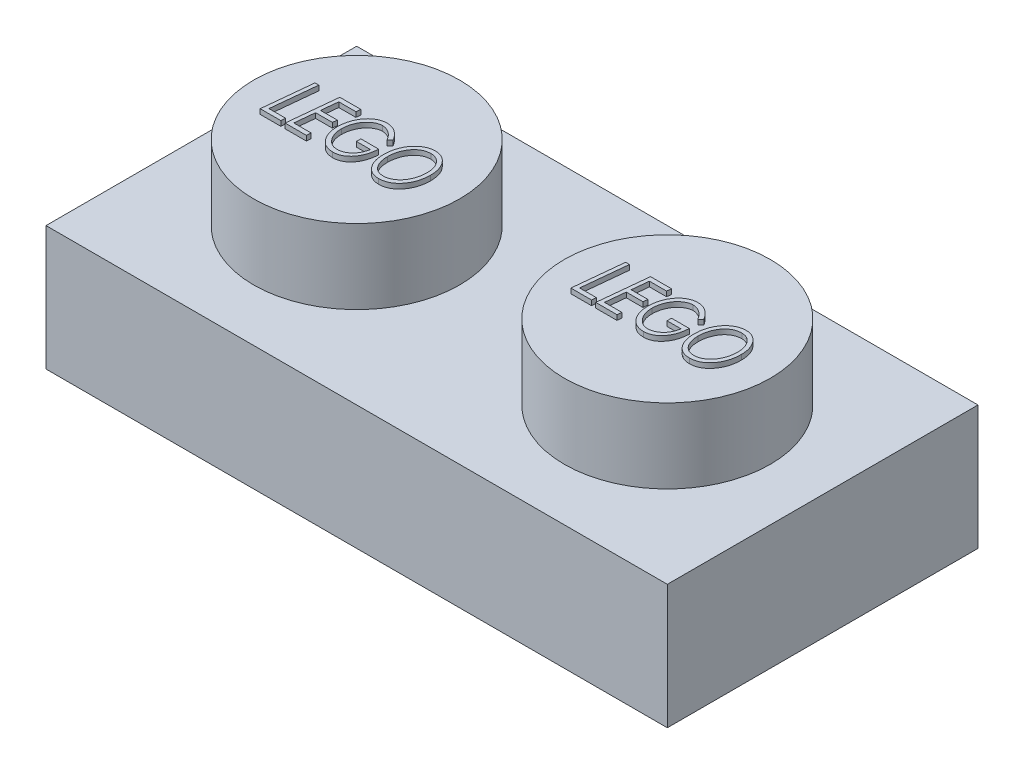
SolidWorks part; units mm, degrees
ref_plane "Front Plane" through (0, 0, 0) normal (0, 0, 1) x (1, 0, 0)
ref_plane "Top Plane" through (0, 0, 0) normal (0, 1, 0) x (1, 0, 0)
ref_plane "Right Plane" through (0, 0, 0) normal (1, 0, 0) x (0, 0, -1)
sketch "Sketch2" plane through (0, 0, 0) normal (0, 1, 0) x (1, 0, 0)
  line L0 (-17.7331, 8.7234) -> (-1.8581, 8.7234)
  line L1 (-1.8581, 8.7234) -> (-1.8581, 0.7859)
  line L2 (-1.8581, 0.7859) -> (-17.7331, 0.7859)
  line L3 (-17.7331, 0.7859) -> (-17.7331, 8.7234)
  dimension "D1" = 15.875
  dimension "D2" = 7.9375
extrude "Boss-Extrude3" add sketch "Sketch2" along normal blind 3.175
sketch "Sketch3" plane through (0, 3.175, 0) normal (0, 1, 0) x (1, 0, 0)
  line L0 (-17.7331, 8.7234) -> (-17.7331, 0.7859) construction
  line L1 (-1.8581, 8.7234) -> (-17.7331, 8.7234) construction
  circle A0 centre (-13.7644, 4.7546) radius 2.6308
  dimension "D1" = 3.9687
  dimension "D2" = 3.9688
extrude "Boss-Extrude4" add sketch "Sketch3" along normal blind 1.905
pattern_linear "LPattern1" count 2 spacing 7.9375 along (1, 0, 0) of "Boss-Extrude4"
shell "Shell1" thickness 1.524
sketch "Sketch4" plane through (0, 5.08, 0) normal (0, 1, 0) x (1, 0, 0)
  line L1 (-13.7644, 4.7546) -> (-13.7644, 4.0766) construction
  line L2 (-15.584, 4.0766) -> (-11.9447, 4.0766) construction
  text T0 "<i>LEGO</i>" font "Century Gothic" height 1.27
  point P4 (-13.7644, 4.7546)
  point P9 (-13.7644, 4.0766)
extrude "Boss-Extrude5" add sketch "Sketch4" along normal blind 0.127
pattern_linear "LPattern2" count 2 spacing 7.9375 along (1, 0, 0) of "Boss-Extrude5"
sketch "Sketch5" plane through (0, 0, 0) normal (0, -1, 0) x (1, 0, 0)
  circle A0 centre (-9.7956, -4.7546) radius 1.4986
  circle A1 centre (-9.7956, -4.7546) radius 0.635
  dimension "D1" = 2.9972
  dimension "D2" = 1.27
extrude "Boss-Extrude6" add sketch "Sketch5" against normal up to surface (1.651 mm away) up to face at (-5.8269, 1.651, -5.8614)
